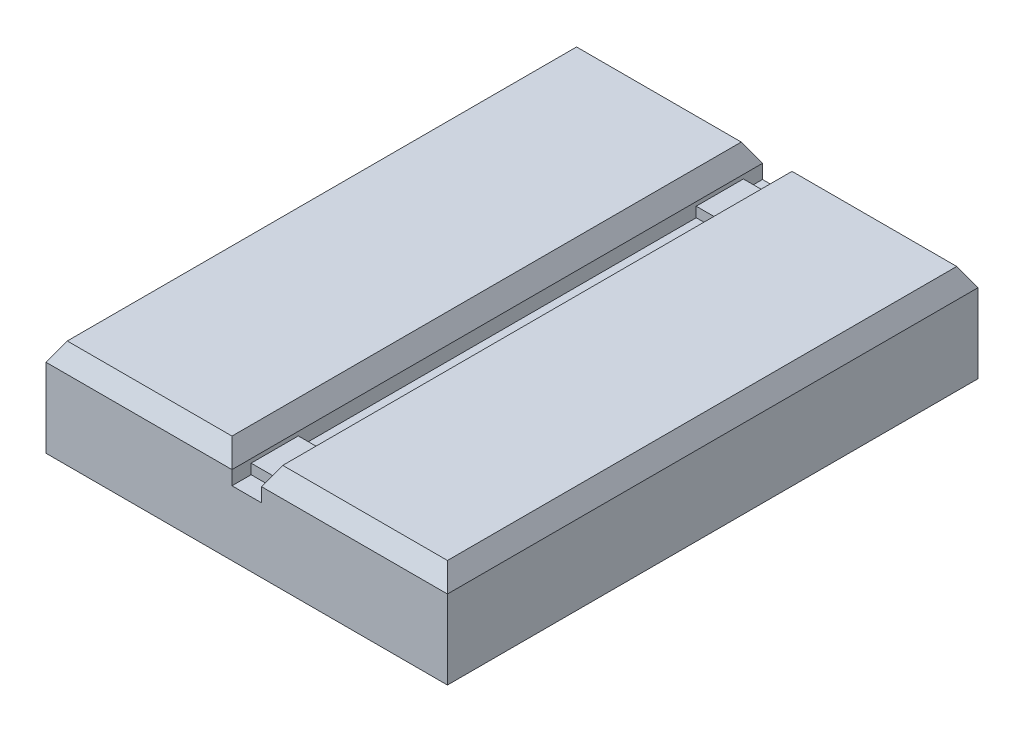
SolidWorks part; units mm, degrees
ref_plane "Front Plane" through (0, 0, 0) normal (0, 0, 1) x (1, 0, 0)
ref_plane "Top Plane" through (0, 0, 0) normal (0, 1, 0) x (1, 0, 0)
ref_plane "Right Plane" through (0, 0, 0) normal (1, 0, 0) x (0, 0, -1)
sketch "Sketch1" plane through (0, 0, 0) normal (0, 0, 1) x (1, 0, 0)
  line L0 (0, 0) -> (0, 42.4008) construction
  line L1 (-17.2974, 0) -> (17.2974, 0)
  line L2 (17.2974, 0) -> (17.2974, 8.382)
  line L3 (1.27, 8.382) -> (1.27, 5.588)
  line L4 (1.27, 5.588) -> (-1.27, 5.588)
  line L5 (1.27, 8.382) -> (17.2974, 8.382)
  line L7 (-1.27, 8.382) -> (-17.2974, 8.382)
  line L8 (-1.27, 8.382) -> (-1.27, 5.588)
  line L9 (-17.2974, 0) -> (-17.2974, 8.382)
  dimension "D1" = 34.5948
  dimension "D2" = 8.382
  dimension "D3" = 2.54
  dimension "D4" = 2.794
extrude "Boss-Extrude1" add sketch "Sketch1" along normal mid plane 45.72
chamfer "Chamfer1" distance 1.5875 angle 30 8 edges at (17.2974, 8.382, 0) (9.2837, 8.382, 22.86) (1.27, 8.382, 0) (9.2837, 8.382, -22.86) (-1.27, 8.382, 0) (-9.2837, 8.382, 22.86) (-17.2974, 8.382, 0) (-9.2837, 8.382, -22.86)
sketch "Sketch2" plane through (0, 0, 0) normal (0, 0, 1) x (1, 0, 0)
  line L0 (-1.27, 6.4516) -> (1.27, 6.4516)
  line L1 (-1.27, 5.588) -> (-1.27, 6.7945) construction
  line L2 (1.27, 6.7945) -> (1.27, 5.588) construction
  line L3 (1.27, 6.4516) -> (1.27, 5.588)
  line L4 (1.27, 5.588) -> (-1.27, 5.588)
  line L5 (-1.27, 5.588) -> (-1.27, 6.4516)
  line L6 (2.1865, 8.382) -> (16.3809, 8.382) construction
  dimension "D1" = 1.9304
extrude "Boss-Extrude2" add sketch "Sketch2" along normal blind 4.064 from offset 17.145
mirror "Mirror1" about plane through (0, 0, 0) normal (0, 0, 1) of "Boss-Extrude2"
sketch "Sketch3" plane through (0, 8.382, 0) normal (0, 1, 0) x (1, 0, 0)
  line L1 (13.2059, 21.3085) -> (14.7934, 21.3085)
  line L2 (13.2059, 21.3085) -> (13.2059, 19.721)
  line L3 (13.2059, 19.721) -> (14.7934, 19.721)
  line L4 (14.7934, 21.3085) -> (14.7934, 19.721)
  line L5 (13.2059, 21.3085) -> (14.7934, 19.721) construction
  line L6 (13.2059, 19.721) -> (14.7934, 21.3085) construction
  line L7 (16.3809, -21.9435) -> (16.3809, 21.9435) construction
  line L8 (16.3809, 21.9435) -> (2.1865, 21.9435) construction
  point P0 (13.9996, 20.5147)
  dimension "D1" = 1.5875
  dimension "D2" = 1.5875
  dimension "D3" = 0.635
